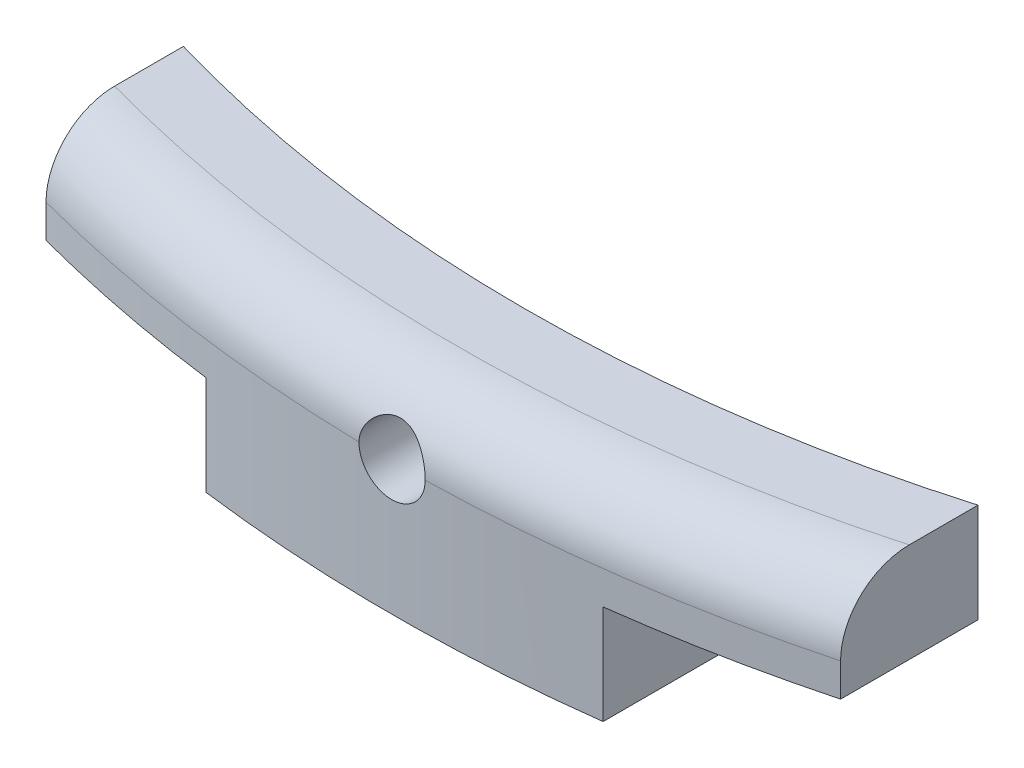
SolidWorks part; units mm, degrees
ref_plane "Front Plane" through (0, 0, 0) normal (0, 0, 1) x (1, 0, 0)
ref_plane "Top Plane" through (0, 0, 0) normal (0, 1, 0) x (1, 0, 0)
ref_plane "Right Plane" through (0, 0, 0) normal (1, 0, 0) x (0, 0, -1)
sketch "Sketch1" plane through (0, 0, 0) normal (0, 1, 0) x (1, 0, 0)
  line L0 (0, -21.5) -> (0, -23.5) construction
  line L3 (3, -23.3077) -> (3, -21.2897)
  line L5 (-3, -23.3077) -> (-3, -21.2897)
  arc A0 (-3, -23.3077) -> (3, -23.3077) centre (0, 0) ccw
  arc A1 (-3, -21.2897) -> (3, -21.2897) centre (0, 0) ccw
  point P6 (0, -22.5)
  dimension "D1" = 43
  dimension "D2" = 47
  dimension "D3" = 3
  dimension "D4" = 3
extrude "Boss-Extrude1" add sketch "Sketch1" along normal blind 3
sketch "Sketch2" plane through (0, 3, 0) normal (0, 1, 0) x (1, 0, 0)
  line L0 (-6, -22.7211) -> (-6, -20.6458)
  line L1 (-3, -21.2897) -> (-3, -23.3077) construction
  line L2 (6, -22.7211) -> (6, -20.6458)
  line L3 (3, -23.3077) -> (3, -21.2897) construction
  arc A0 (-6, -22.7211) -> (6, -22.7211) centre (0, 0) ccw
  arc A2 (-6, -20.6458) -> (6, -20.6458) centre (0, 0) ccw
  arc A3 (-3, -21.2897) -> (3, -21.2897) centre (0, 0) ccw construction
  arc A4 (-3, -23.3077) -> (3, -23.3077) centre (0, 0) ccw construction
  dimension "D2" = 3
  dimension "D3" = 3
extrude "Boss-Extrude2" add sketch "Sketch2" against normal blind 1.5
fillet "Fillet1" radius 1 1 edges at (0, 3, 23.5)
sketch "Sketch3" plane through (0, 0, 0) normal (0, 0, 1) x (1, 0, 0)
  line L0 (-3, 0) -> (3, 0) construction
  circle A0 centre (0, 2) radius 0.5
  point P4 (0, 0)
  dimension "D1" = 1
  dimension "D2" = 2
extrude "Cut-Extrude1" cut sketch "Sketch3" along normal up to next
